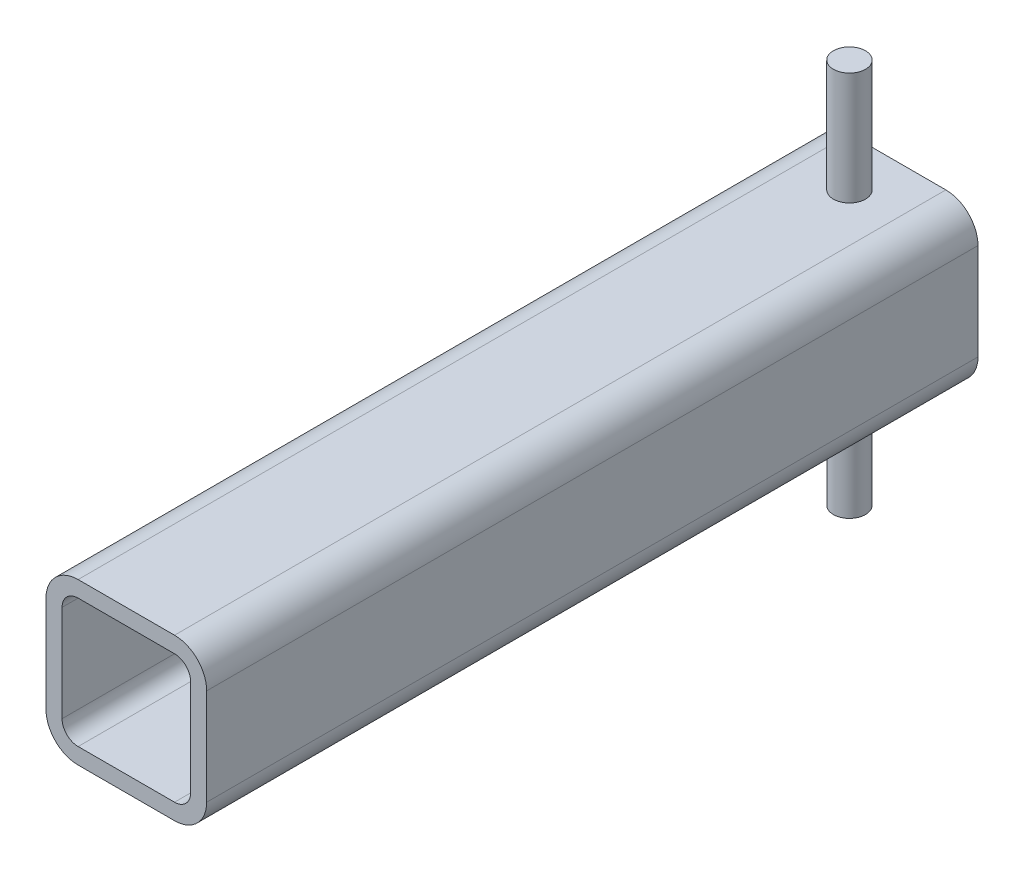
SolidWorks part; units mm, degrees
ref_plane "Front Plane" through (0, 0, 0) normal (0, 0, 1) x (1, 0, 0)
ref_plane "Top Plane" through (0, 0, 0) normal (0, 1, 0) x (1, 0, 0)
ref_plane "Right Plane" through (0, 0, 0) normal (1, 0, 0) x (0, 0, -1)
sketch "Sketch1" plane through (0, 0, 0) normal (0, 0, 1) x (1, 0, 0)
  line L0 (-19.05, -25.4) -> (19.05, -25.4)
  line L1 (-25.4, -19.05) -> (-25.4, 19.05)
  line L2 (19.05, 25.4) -> (-19.05, 25.4)
  line L3 (25.4, 19.05) -> (25.4, -19.05)
  line L4 (-19.05, -31.75) -> (19.05, -31.75)
  line L5 (-31.75, -19.05) -> (-31.75, 19.05)
  line L6 (19.05, 31.75) -> (-19.05, 31.75)
  line L7 (31.75, 19.05) -> (31.75, -19.05)
  line L10 (-25.4, 0) -> (25.4, 0)
  arc A0 (31.75, 19.05) -> (19.05, 31.75) centre (19.05, 19.05) ccw
  arc A1 (19.05, -31.75) -> (31.75, -19.05) centre (19.05, -19.05) ccw
  arc A2 (-31.75, -19.05) -> (-19.05, -31.75) centre (-19.05, -19.05) ccw
  arc A3 (-19.05, 31.75) -> (-31.75, 19.05) centre (-19.05, 19.05) ccw
  arc A4 (-19.05, 25.4) -> (-25.4, 19.05) centre (-19.05, 19.05) ccw
  arc A5 (25.4, 19.05) -> (19.05, 25.4) centre (19.05, 19.05) ccw
  arc A6 (19.05, -25.4) -> (25.4, -19.05) centre (19.05, -19.05) ccw
  arc A7 (-25.4, -19.05) -> (-19.05, -25.4) centre (-19.05, -19.05) ccw
extrude "Boss-Extrude1" add sketch "Sketch1" along normal blind 304.8 contours L6 A3 L5 A2 L4 A1 L7 A0 A7 L1 A4 L2 A5 L3 A6 L0
sketch "Sketch3" plane through (0, 0, 0) normal (0, 1, 0) x (1, 0, 0)
  line L0 (0, -34.925) -> (0, 34.925) construction
  line L1 (-34.925, 0) -> (34.925, 0) construction
  circle A0 centre (0, -19.05) radius 6.35
  dimension "D2" = 12.7
  dimension "D1" = 19.05
extrude "Boss-Extrude2" add sketch "Sketch3" along normal mid plane 152.4
